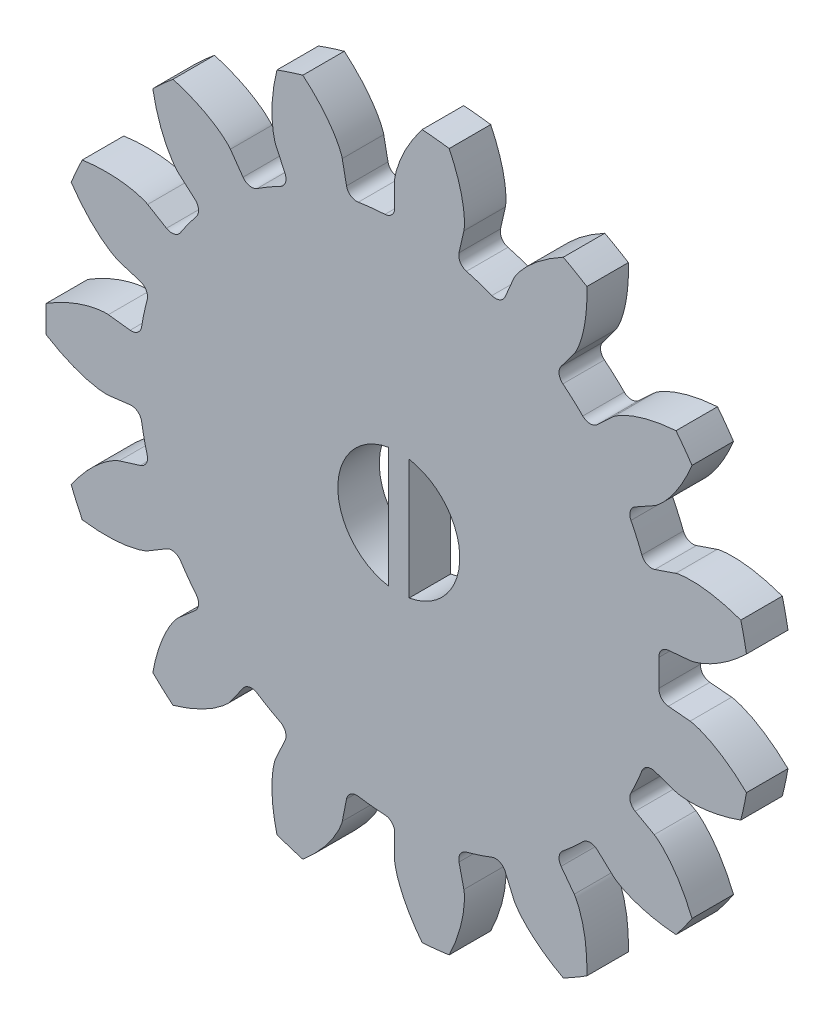
SolidWorks part; units mm, degrees
ref_plane "Front Plane" through (0, 0, 0) normal (0, 0, 1) x (1, 0, 0)
ref_plane "Top Plane" through (0, 0, 0) normal (0, 1, 0) x (1, 0, 0)
ref_plane "Right Plane" through (0, 0, 0) normal (1, 0, 0) x (0, 0, -1)
sketch "Model" plane through (0, 0, 0) normal (0, 0, 1) x (1, 0, 0)
  line L0 (-54.4812, -102.8312) -> (-54.9244, -103.7899)
  line L1 (-51.7248, -104.8295) -> (-51.5198, -103.7934)
  line L2 (-49.1951, -104.0377) -> (-49.2101, -105.0938)
  line L3 (-39.4416, -99.869) -> (-38.6668, -100.5867)
  line L4 (-40.5459, -102.2787) -> (-41.1787, -101.4331)
  line L5 (-57.1142, -102.5256) -> (-56.5055, -101.6625)
  line L6 (-43.8753, -102.9899) -> (-43.4594, -103.9608)
  line L7 (-58.8195, -99.5789) -> (-59.6143, -100.2745)
  line L8 (-45.8642, -104.7422) -> (-46.0984, -103.7123)
  line L9 (-36.6607, -95.2145) -> (-35.6609, -95.555)
  line L10 (-36.6894, -97.865) -> (-37.6114, -97.3499)
  line L11 (-36.0133, -89.8313) -> (-34.9614, -89.7357)
  line L12 (-34.9614, -92.2643) -> (-36.0133, -92.1687)
  line L13 (-51.5198, -78.2066) -> (-51.7248, -77.1705)
  line L14 (-54.9244, -78.2101) -> (-54.4812, -79.1688)
  line L15 (-49.2101, -76.9062) -> (-49.1951, -77.9623)
  line L16 (-56.5055, -80.3375) -> (-57.1142, -79.4744)
  line L17 (-62.4689, -86.8446) -> (-61.4599, -87.1567)
  line L18 (-60.1934, -84.3121) -> (-61.1006, -83.7712)
  line L19 (-61.4599, -94.8433) -> (-62.4689, -95.1554)
  line L20 (-62.9947, -92.6821) -> (-61.9459, -92.5569)
  line L21 (-59.6143, -81.7255) -> (-58.8195, -82.4211)
  line L22 (-61.9459, -89.4431) -> (-62.9947, -89.3179)
  line L23 (-61.1006, -98.2288) -> (-60.1934, -97.6879)
  line L24 (-43.4594, -78.0392) -> (-43.8753, -79.0101)
  line L25 (-46.0984, -78.2877) -> (-45.8642, -77.2578)
  line L26 (-38.6668, -81.4133) -> (-39.4416, -82.131)
  line L27 (-35.6609, -86.445) -> (-36.6607, -86.7855)
  line L28 (-37.6114, -84.6501) -> (-36.6894, -84.135)
  line L29 (-41.1787, -80.5669) -> (-40.5459, -79.7213)
  line L30 (-48.5, -93.8946) -> (-48.5, -88.1054)
  line L31 (-49.5, -88.1054) -> (-49.5, -93.8946)
  arc A0 (-55.825, -101.531) -> (-54.7076, -102.1761) centre (-49, -91) ccw
  arc A1 (-45.7407, -103.1186) -> (-46.0984, -103.7123) centre (-45.6109, -103.6014) ccw
  arc A2 (-54.4812, -102.8312) -> (-54.7076, -102.1761) centre (-54.935, -102.6214) ccw
  arc A3 (-50.9516, -103.3965) -> (-51.5198, -103.7934) centre (-51.0293, -103.8904) ccw
  arc A4 (-43.8753, -102.9899) -> (-44.5137, -102.7199) centre (-44.3349, -103.1868) ccw
  arc A5 (-41.0934, -100.7452) -> (-40.1347, -99.8819) centre (-49, -91) ccw
  arc A6 (-41.0746, -106.0396) -> (-39.938, -105.3833) centre (-49, -91) ccw
  arc A7 (-54.8735, -106.9531) -> (-53.6253, -107.3587) centre (-49, -91) ccw
  arc A8 (-35.6427, -101.5158) -> (-34.8712, -100.454) centre (-49, -91) ccw
  arc A9 (-41.0934, -100.7452) -> (-41.1787, -101.4331) centre (-40.7784, -101.1335) ccw
  arc A10 (-37.8133, -96.6868) -> (-37.6114, -97.3499) centre (-37.3676, -96.9134) ccw
  arc A11 (-55.825, -101.531) -> (-56.5055, -101.6625) centre (-56.0969, -101.9506) ccw
  arc A12 (-45.7407, -103.1186) -> (-44.5137, -102.7199) centre (-49, -91) ccw
  arc A13 (-59.5183, -97.8446) -> (-58.7599, -98.8884) centre (-49, -91) ccw
  arc A14 (-50.9516, -103.3965) -> (-49.6685, -103.5314) centre (-49, -91) ccw
  arc A15 (-58.8195, -99.5789) -> (-58.7599, -98.8884) centre (-59.1488, -99.2027) ccw
  arc A16 (-47.877, -107.9629) -> (-46.5717, -107.8257) centre (-49, -91) ccw
  arc A17 (-60.8544, -103.1849) -> (-59.8791, -104.0631) centre (-49, -91) ccw
  arc A18 (-37.8133, -96.6868) -> (-37.2885, -95.5081) centre (-49, -91) ccw
  arc A19 (-32.5203, -95.1738) -> (-32.2474, -93.89) centre (-49, -91) ccw
  arc A20 (-32.2474, -88.11) -> (-32.5203, -86.8262) centre (-49, -91) ccw
  arc A21 (-39.4416, -99.869) -> (-40.1347, -99.8819) centre (-39.7814, -100.2358) ccw
  arc A22 (-36.6607, -95.2145) -> (-37.2885, -95.5081) centre (-36.8219, -95.6878) ccw
  arc A23 (-49.1951, -104.0377) -> (-49.6685, -103.5314) centre (-49.6951, -104.0307) ccw
  arc A24 (-36.0133, -89.8313) -> (-36.4674, -90.3549) centre (-35.9681, -90.3292) ccw
  arc A25 (-36.4674, -91.6451) -> (-36.4674, -90.3549) centre (-49, -91) ccw
  arc A26 (-36.4674, -91.6451) -> (-36.0133, -92.1687) centre (-35.9681, -91.6708) ccw
  arc A27 (-49.6685, -78.4686) -> (-49.1951, -77.9623) centre (-49.6951, -77.9693) ccw
  arc A28 (-51.5198, -78.2066) -> (-50.9516, -78.6035) centre (-51.0293, -78.1096) ccw
  arc A29 (-53.6253, -74.6413) -> (-54.8735, -75.0469) centre (-49, -91) ccw
  arc A30 (-54.7076, -79.8239) -> (-54.4812, -79.1688) centre (-54.935, -79.3786) ccw
  arc A31 (-54.7076, -79.8239) -> (-55.825, -80.469) centre (-49, -91) ccw
  arc A32 (-56.5055, -80.3375) -> (-55.825, -80.469) centre (-56.0969, -80.0494) ccw
  arc A33 (-49.6685, -78.4686) -> (-50.9516, -78.6035) centre (-49, -91) ccw
  arc A34 (-46.5717, -74.1743) -> (-47.877, -74.0371) centre (-49, -91) ccw
  arc A35 (-58.7599, -83.1116) -> (-59.5183, -84.1554) centre (-49, -91) ccw
  arc A36 (-61.3929, -92.9747) -> (-61.9459, -92.5569) centre (-61.8866, -93.0534) ccw
  arc A37 (-61.3929, -92.9747) -> (-61.1246, -94.2367) centre (-49, -91) ccw
  arc A38 (-58.7599, -83.1116) -> (-58.8195, -82.4211) centre (-59.1488, -82.7973) ccw
  arc A39 (-61.9459, -89.4431) -> (-61.3929, -89.0253) centre (-61.8866, -88.9466) ccw
  arc A40 (-59.8791, -77.9369) -> (-60.8544, -78.8151) centre (-49, -91) ccw
  arc A41 (-64.2518, -83.4911) -> (-64.7856, -84.6901) centre (-49, -91) ccw
  arc A42 (-61.1246, -87.7633) -> (-61.4599, -87.1567) centre (-61.6077, -87.6344) ccw
  arc A43 (-65.9873, -90.3438) -> (-65.9873, -91.6562) centre (-49, -91) ccw
  arc A44 (-61.1246, -87.7633) -> (-61.3929, -89.0253) centre (-49, -91) ccw
  arc A45 (-60.1934, -84.3121) -> (-59.5183, -84.1554) centre (-59.9374, -83.8827) ccw
  arc A46 (-61.4599, -94.8433) -> (-61.1246, -94.2367) centre (-61.6077, -94.3656) ccw
  arc A47 (-59.5183, -97.8446) -> (-60.1934, -97.6879) centre (-59.9374, -98.1173) ccw
  arc A48 (-46.0984, -78.2877) -> (-45.7407, -78.8814) centre (-45.6109, -78.3986) ccw
  arc A49 (-39.938, -76.6167) -> (-41.0746, -75.9604) centre (-49, -91) ccw
  arc A50 (-44.5137, -79.2801) -> (-45.7407, -78.8814) centre (-49, -91) ccw
  arc A51 (-44.5137, -79.2801) -> (-43.8753, -79.0101) centre (-44.3349, -78.8132) ccw
  arc A52 (-37.2885, -86.4919) -> (-36.6607, -86.7855) centre (-36.8219, -86.3122) ccw
  arc A53 (-64.7856, -97.3099) -> (-64.2518, -98.5089) centre (-49, -91) ccw
  arc A54 (-37.6114, -84.6501) -> (-37.8133, -85.3132) centre (-37.3676, -85.0866) ccw
  arc A55 (-37.2885, -86.4919) -> (-37.8133, -85.3132) centre (-49, -91) ccw
  arc A56 (-40.1347, -82.1181) -> (-39.4416, -82.131) centre (-39.7814, -81.7642) ccw
  arc A57 (-34.8712, -81.546) -> (-35.6427, -80.4842) centre (-49, -91) ccw
  arc A58 (-40.1347, -82.1181) -> (-41.0934, -81.2548) centre (-49, -91) ccw
  arc A59 (-41.1787, -80.5669) -> (-41.0934, -81.2548) centre (-40.7784, -80.8665) ccw
  arc A60 (-48.5, -93.8946) -> (-48.5, -88.1054) centre (-49, -91) ccw
  arc A61 (-49.5, -88.1054) -> (-49.5, -93.8946) centre (-49, -91) ccw
  spline S0 degree 5 poles (-54.9244, -103.7899) (-54.9388, -103.8212) (-54.9546, -103.8611) (-54.9775, -103.9347) (-54.9977, -104.0186) (-55.0256, -104.1367) (-55.0449, -104.2305) (-55.0644, -104.3516) (-55.078, -104.4564) (-55.0915, -104.5796) (-55.1037, -104.7214) (-55.1126, -104.9005) (-55.1163, -105.0811) (-55.113, -105.2998) (-55.1005, -105.5479) (-55.0799, -105.7886) (-55.0514, -106.0308) (-55.0132, -106.2836) (-54.9706, -106.5187) (-54.9333, -106.6979) (-54.9032, -106.8302) (-54.8828, -106.9153) (-54.8735, -106.9531) knots 0 0 0 0 0 0 0.057143 0.071429 0.128571 0.142857 0.2 0.214286 0.271429 0.3 0.342857 0.428571 0.5 0.557143 0.642857 0.728571 0.8 0.871429 0.942857 1 1 1 1 1 1
  spline S1 degree 5 poles (-49.2101, -105.0938) (-49.2106, -105.1283) (-49.2087, -105.1711) (-49.1997, -105.2477) (-49.184, -105.3326) (-49.1614, -105.4518) (-49.141, -105.5454) (-49.1095, -105.6639) (-49.0793, -105.7652) (-49.0416, -105.8832) (-48.995, -106.0177) (-48.9303, -106.1849) (-48.8602, -106.3514) (-48.7683, -106.5499) (-48.6559, -106.7714) (-48.5392, -106.983) (-48.4147, -107.1926) (-48.2769, -107.4081) (-48.1424, -107.6055) (-48.0354, -107.754) (-47.9541, -107.8626) (-47.9008, -107.9321) (-47.877, -107.9629) knots 0 0 0 0 0 0 0.057143 0.071429 0.128571 0.142857 0.2 0.214286 0.271429 0.3 0.342857 0.428571 0.5 0.557143 0.642857 0.728571 0.8 0.871429 0.942857 1 1 1 1 1 1
  spline S2 degree 5 poles (-45.8642, -104.7422) (-45.8566, -104.7758) (-45.8495, -104.8181) (-45.8424, -104.8949) (-45.8401, -104.9811) (-45.8374, -105.1024) (-45.838, -105.1982) (-45.8441, -105.3207) (-45.8525, -105.4261) (-45.8649, -105.5493) (-45.8825, -105.6906) (-45.9111, -105.8676) (-45.945, -106.045) (-45.9936, -106.2583) (-46.0575, -106.4983) (-46.1276, -106.7295) (-46.2059, -106.9605) (-46.2959, -107.1998) (-46.3864, -107.4209) (-46.4602, -107.5884) (-46.5171, -107.7116) (-46.5548, -107.7906) (-46.5717, -107.8257) knots 0 0 0 0 0 0 0.057143 0.071429 0.128571 0.142857 0.2 0.214286 0.271429 0.3 0.342857 0.428571 0.5 0.557143 0.642857 0.728571 0.8 0.871429 0.942857 1 1 1 1 1 1
  spline S3 degree 5 poles (-38.6668, -100.5867) (-38.6415, -100.6101) (-38.6084, -100.6374) (-38.5455, -100.682) (-38.4719, -100.7271) (-38.3682, -100.7901) (-38.285, -100.8375) (-38.1758, -100.8934) (-38.0804, -100.9388) (-37.9674, -100.9897) (-37.8364, -101.0451) (-37.6688, -101.1089) (-37.4982, -101.1682) (-37.2892, -101.2327) (-37.0493, -101.2975) (-36.814, -101.3523) (-36.5749, -101.4) (-36.3226, -101.4418) (-36.0859, -101.4739) (-35.9039, -101.4938) (-35.7688, -101.506) (-35.6815, -101.5129) (-35.6427, -101.5158) knots 0 0 0 0 0 0 0.057143 0.071429 0.128571 0.142857 0.2 0.214286 0.271429 0.3 0.342857 0.428571 0.5 0.557143 0.642857 0.728571 0.8 0.871429 0.942857 1 1 1 1 1 1
  spline S4 degree 5 poles (-51.7248, -104.8295) (-51.7315, -104.8633) (-51.7422, -104.9048) (-51.7669, -104.9779) (-51.7999, -105.0576) (-51.8468, -105.1696) (-51.8863, -105.2568) (-51.9417, -105.3662) (-51.9923, -105.4591) (-52.0537, -105.5666) (-52.1272, -105.6885) (-52.2253, -105.8386) (-52.3285, -105.9869) (-52.4596, -106.1619) (-52.6156, -106.3553) (-52.7737, -106.5379) (-52.9392, -106.7171) (-53.1187, -106.8992) (-53.2914, -107.0643) (-53.4269, -107.1873) (-53.529, -107.2767) (-53.5955, -107.3335) (-53.6253, -107.3587) knots 0 0 0 0 0 0 0.057143 0.071429 0.128571 0.142857 0.2 0.214286 0.271429 0.3 0.342857 0.428571 0.5 0.557143 0.642857 0.728571 0.8 0.871429 0.942857 1 1 1 1 1 1
  spline S5 degree 5 poles (-57.1142, -102.5256) (-57.134, -102.5538) (-57.1607, -102.5873) (-57.2131, -102.644) (-57.2756, -102.7035) (-57.364, -102.7866) (-57.4355, -102.8503) (-57.5307, -102.9277) (-57.6146, -102.9919) (-57.7145, -103.0652) (-57.8312, -103.1466) (-57.9819, -103.2439) (-58.1364, -103.3374) (-58.3274, -103.4439) (-58.5486, -103.5571) (-58.7673, -103.6597) (-58.9913, -103.756) (-59.2294, -103.8494) (-59.4543, -103.93) (-59.6281, -103.9873) (-59.7577, -104.0274) (-59.8416, -104.0523) (-59.8791, -104.0631) knots 0 0 0 0 0 0 0.057143 0.071429 0.128571 0.142857 0.2 0.214286 0.271429 0.3 0.342857 0.428571 0.5 0.557143 0.642857 0.728571 0.8 0.871429 0.942857 1 1 1 1 1 1
  spline S6 degree 5 poles (-40.5459, -102.2787) (-40.5253, -102.3062) (-40.5016, -102.342) (-40.4638, -102.4093) (-40.4267, -102.4871) (-40.3748, -102.5969) (-40.3364, -102.6846) (-40.2922, -102.799) (-40.257, -102.8987) (-40.2182, -103.0163) (-40.1768, -103.1525) (-40.1309, -103.3258) (-40.0897, -103.5017) (-40.0475, -103.7163) (-40.0081, -103.9616) (-39.9782, -104.2013) (-39.9558, -104.4441) (-39.9406, -104.6994) (-39.9334, -104.9382) (-39.9326, -105.1213) (-39.9345, -105.2569) (-39.9368, -105.3444) (-39.938, -105.3833) knots 0 0 0 0 0 0 0.057143 0.071429 0.128571 0.142857 0.2 0.214286 0.271429 0.3 0.342857 0.428571 0.5 0.557143 0.642857 0.728571 0.8 0.871429 0.942857 1 1 1 1 1 1
  spline S7 degree 5 poles (-43.4594, -103.9608) (-43.4459, -103.9925) (-43.4267, -104.0308) (-43.3874, -104.0972) (-43.3385, -104.1683) (-43.2694, -104.268) (-43.2126, -104.3452) (-43.1357, -104.4407) (-43.0669, -104.521) (-42.9844, -104.6134) (-42.8872, -104.7173) (-42.7601, -104.8438) (-42.6283, -104.9674) (-42.4636, -105.1113) (-42.2709, -105.268) (-42.0782, -105.4138) (-41.8791, -105.5546) (-41.6657, -105.6954) (-41.4625, -105.821) (-41.3043, -105.9132) (-41.1859, -105.9794) (-41.109, -106.0211) (-41.0746, -106.0396) knots 0 0 0 0 0 0 0.057143 0.071429 0.128571 0.142857 0.2 0.214286 0.271429 0.3 0.342857 0.428571 0.5 0.557143 0.642857 0.728571 0.8 0.871429 0.942857 1 1 1 1 1 1
  spline S8 degree 5 poles (-35.6609, -95.555) (-35.6283, -95.5661) (-35.587, -95.5776) (-35.5113, -95.5927) (-35.4258, -95.604) (-35.3054, -95.6194) (-35.2101, -95.6288) (-35.0876, -95.6355) (-34.982, -95.6382) (-34.8581, -95.6387) (-34.7158, -95.636) (-34.5367, -95.6261) (-34.3567, -95.6109) (-34.1396, -95.5848) (-33.8941, -95.5464) (-33.6569, -95.5008) (-33.419, -95.4471) (-33.1716, -95.3827) (-32.9422, -95.3157) (-32.7679, -95.2599) (-32.6395, -95.2161) (-32.557, -95.1869) (-32.5203, -95.1738) knots 0 0 0 0 0 0 0.057143 0.071429 0.128571 0.142857 0.2 0.214286 0.271429 0.3 0.342857 0.428571 0.5 0.557143 0.642857 0.728571 0.8 0.871429 0.942857 1 1 1 1 1 1
  spline S9 degree 5 poles (-36.6894, -97.865) (-36.6593, -97.8818) (-36.6231, -97.9048) (-36.5613, -97.9509) (-36.4956, -98.0069) (-36.4037, -98.0861) (-36.3329, -98.1506) (-36.246, -98.2371) (-36.1733, -98.3139) (-36.09, -98.4056) (-35.9968, -98.5132) (-35.8843, -98.6528) (-35.7752, -98.7968) (-35.6493, -98.9756) (-35.5136, -99.1837) (-35.3887, -99.3905) (-35.2695, -99.6032) (-35.1517, -99.8302) (-35.0481, -100.0455) (-34.9729, -100.2124) (-34.9195, -100.3371) (-34.886, -100.4179) (-34.8712, -100.454) knots 0 0 0 0 0 0 0.057143 0.071429 0.128571 0.142857 0.2 0.214286 0.271429 0.3 0.342857 0.428571 0.5 0.557143 0.642857 0.728571 0.8 0.871429 0.942857 1 1 1 1 1 1
  spline S10 degree 5 poles (-34.9614, -89.7357) (-34.9271, -89.7326) (-34.8847, -89.7263) (-34.8094, -89.7093) (-34.7267, -89.6848) (-34.6105, -89.6499) (-34.5196, -89.6198) (-34.405, -89.5761) (-34.3074, -89.5355) (-34.194, -89.4856) (-34.0651, -89.4253) (-33.9055, -89.3434) (-33.7473, -89.2563) (-33.5595, -89.1442) (-33.3509, -89.0093) (-33.1527, -88.8711) (-32.9573, -88.7253) (-32.7574, -88.5658) (-32.5751, -88.4113) (-32.4386, -88.2894) (-32.3391, -88.1972) (-32.2756, -88.137) (-32.2474, -88.11) knots 0 0 0 0 0 0 0.057143 0.071429 0.128571 0.142857 0.2 0.214286 0.271429 0.3 0.342857 0.428571 0.5 0.557143 0.642857 0.728571 0.8 0.871429 0.942857 1 1 1 1 1 1
  spline S11 degree 5 poles (-34.9614, -92.2643) (-34.9271, -92.2674) (-34.8847, -92.2737) (-34.8094, -92.2907) (-34.7267, -92.3152) (-34.6105, -92.3501) (-34.5196, -92.3802) (-34.405, -92.4239) (-34.3074, -92.4645) (-34.194, -92.5144) (-34.0651, -92.5747) (-33.9055, -92.6566) (-33.7473, -92.7437) (-33.5595, -92.8558) (-33.3509, -92.9907) (-33.1527, -93.1289) (-32.9573, -93.2747) (-32.7574, -93.4342) (-32.5751, -93.5887) (-32.4386, -93.7106) (-32.3391, -93.8028) (-32.2756, -93.863) (-32.2474, -93.89) knots 0 0 0 0 0 0 0.057143 0.071429 0.128571 0.142857 0.2 0.214286 0.271429 0.3 0.342857 0.428571 0.5 0.557143 0.642857 0.728571 0.8 0.871429 0.942857 1 1 1 1 1 1
  spline S12 degree 5 poles (-45.8642, -77.2578) (-45.8566, -77.2242) (-45.8495, -77.1819) (-45.8424, -77.1051) (-45.8401, -77.0189) (-45.8374, -76.8976) (-45.838, -76.8018) (-45.8441, -76.6793) (-45.8525, -76.5739) (-45.8649, -76.4507) (-45.8825, -76.3094) (-45.9111, -76.1324) (-45.945, -75.955) (-45.9936, -75.7417) (-46.0575, -75.5017) (-46.1276, -75.2705) (-46.2059, -75.0395) (-46.2959, -74.8002) (-46.3864, -74.5791) (-46.4602, -74.4116) (-46.5171, -74.2884) (-46.5548, -74.2094) (-46.5717, -74.1743) knots 0 0 0 0 0 0 0.057143 0.071429 0.128571 0.142857 0.2 0.214286 0.271429 0.3 0.342857 0.428571 0.5 0.557143 0.642857 0.728571 0.8 0.871429 0.942857 1 1 1 1 1 1
  spline S13 degree 5 poles (-49.2101, -76.9062) (-49.2106, -76.8717) (-49.2087, -76.8289) (-49.1997, -76.7523) (-49.184, -76.6674) (-49.1614, -76.5482) (-49.141, -76.4546) (-49.1095, -76.3361) (-49.0793, -76.2348) (-49.0416, -76.1168) (-48.995, -75.9823) (-48.9303, -75.8151) (-48.8602, -75.6486) (-48.7683, -75.4501) (-48.6559, -75.2286) (-48.5392, -75.017) (-48.4147, -74.8074) (-48.2769, -74.5919) (-48.1424, -74.3945) (-48.0354, -74.246) (-47.9541, -74.1374) (-47.9008, -74.0679) (-47.877, -74.0371) knots 0 0 0 0 0 0 0.057143 0.071429 0.128571 0.142857 0.2 0.214286 0.271429 0.3 0.342857 0.428571 0.5 0.557143 0.642857 0.728571 0.8 0.871429 0.942857 1 1 1 1 1 1
  spline S14 degree 5 poles (-54.9244, -78.2101) (-54.9388, -78.1788) (-54.9546, -78.1389) (-54.9775, -78.0653) (-54.9977, -77.9814) (-55.0256, -77.8633) (-55.0449, -77.7695) (-55.0644, -77.6484) (-55.078, -77.5436) (-55.0915, -77.4204) (-55.1037, -77.2786) (-55.1126, -77.0995) (-55.1163, -76.9189) (-55.113, -76.7002) (-55.1005, -76.4521) (-55.0799, -76.2114) (-55.0514, -75.9692) (-55.0132, -75.7164) (-54.9706, -75.4813) (-54.9333, -75.3021) (-54.9032, -75.1698) (-54.8828, -75.0847) (-54.8735, -75.0469) knots 0 0 0 0 0 0 0.057143 0.071429 0.128571 0.142857 0.2 0.214286 0.271429 0.3 0.342857 0.428571 0.5 0.557143 0.642857 0.728571 0.8 0.871429 0.942857 1 1 1 1 1 1
  spline S15 degree 5 poles (-51.7248, -77.1705) (-51.7315, -77.1367) (-51.7422, -77.0952) (-51.7669, -77.0221) (-51.7999, -76.9424) (-51.8468, -76.8304) (-51.8863, -76.7432) (-51.9417, -76.6338) (-51.9923, -76.5409) (-52.0537, -76.4334) (-52.1272, -76.3115) (-52.2253, -76.1614) (-52.3285, -76.0131) (-52.4596, -75.8381) (-52.6156, -75.6447) (-52.7737, -75.4621) (-52.9392, -75.2829) (-53.1187, -75.1008) (-53.2914, -74.9357) (-53.4269, -74.8127) (-53.529, -74.7233) (-53.5955, -74.6665) (-53.6253, -74.6413) knots 0 0 0 0 0 0 0.057143 0.071429 0.128571 0.142857 0.2 0.214286 0.271429 0.3 0.342857 0.428571 0.5 0.557143 0.642857 0.728571 0.8 0.871429 0.942857 1 1 1 1 1 1
  spline S16 degree 5 poles (-57.1142, -79.4744) (-57.134, -79.4462) (-57.1607, -79.4127) (-57.2131, -79.356) (-57.2756, -79.2965) (-57.364, -79.2134) (-57.4355, -79.1497) (-57.5307, -79.0723) (-57.6146, -79.0081) (-57.7145, -78.9348) (-57.8312, -78.8534) (-57.9819, -78.7561) (-58.1364, -78.6626) (-58.3274, -78.5561) (-58.5486, -78.4429) (-58.7673, -78.3403) (-58.9913, -78.244) (-59.2294, -78.1506) (-59.4543, -78.07) (-59.6281, -78.0127) (-59.7577, -77.9726) (-59.8416, -77.9477) (-59.8791, -77.9369) knots 0 0 0 0 0 0 0.057143 0.071429 0.128571 0.142857 0.2 0.214286 0.271429 0.3 0.342857 0.428571 0.5 0.557143 0.642857 0.728571 0.8 0.871429 0.942857 1 1 1 1 1 1
  spline S17 degree 5 poles (-61.1006, -83.7712) (-61.1302, -83.7535) (-61.1682, -83.7337) (-61.2391, -83.7032) (-61.3204, -83.6744) (-61.4349, -83.6343) (-61.5262, -83.6052) (-61.6446, -83.5732) (-61.7474, -83.5487) (-61.8685, -83.5224) (-62.0082, -83.4955) (-62.1854, -83.4679) (-62.3646, -83.4453) (-62.5824, -83.4257) (-62.8305, -83.4122) (-63.072, -83.4075) (-63.3159, -83.4106) (-63.5713, -83.4222) (-63.8096, -83.44) (-63.9917, -83.4584) (-64.1264, -83.4745) (-64.2132, -83.4859) (-64.2518, -83.4911) knots 0 0 0 0 0 0 0.057143 0.071429 0.128571 0.142857 0.2 0.214286 0.271429 0.3 0.342857 0.428571 0.5 0.557143 0.642857 0.728571 0.8 0.871429 0.942857 1 1 1 1 1 1
  spline S18 degree 5 poles (-62.9947, -89.3179) (-63.0289, -89.3138) (-63.0717, -89.3112) (-63.1488, -89.3121) (-63.2348, -89.3188) (-63.3558, -89.3288) (-63.451, -89.3394) (-63.5721, -89.3583) (-63.676, -89.3777) (-63.7973, -89.4029) (-63.9359, -89.4352) (-64.109, -89.4821) (-64.2819, -89.5343) (-64.4889, -89.605) (-64.721, -89.6936) (-64.9436, -89.7875) (-65.1651, -89.8895) (-65.3938, -90.004) (-65.6041, -90.1172) (-65.7631, -90.2081) (-65.8796, -90.2775) (-65.9542, -90.3232) (-65.9873, -90.3438) knots 0 0 0 0 0 0 0.057143 0.071429 0.128571 0.142857 0.2 0.214286 0.271429 0.3 0.342857 0.428571 0.5 0.557143 0.642857 0.728571 0.8 0.871429 0.942857 1 1 1 1 1 1
  spline S19 degree 5 poles (-62.9947, -92.6821) (-63.0289, -92.6862) (-63.0717, -92.6888) (-63.1488, -92.6879) (-63.2348, -92.6812) (-63.3558, -92.6712) (-63.451, -92.6606) (-63.5721, -92.6417) (-63.676, -92.6223) (-63.7973, -92.5971) (-63.9359, -92.5648) (-64.109, -92.5179) (-64.2819, -92.4657) (-64.4889, -92.395) (-64.721, -92.3064) (-64.9436, -92.2125) (-65.1651, -92.1105) (-65.3938, -91.996) (-65.6041, -91.8828) (-65.7631, -91.7919) (-65.8796, -91.7225) (-65.9542, -91.6768) (-65.9873, -91.6562) knots 0 0 0 0 0 0 0.057143 0.071429 0.128571 0.142857 0.2 0.214286 0.271429 0.3 0.342857 0.428571 0.5 0.557143 0.642857 0.728571 0.8 0.871429 0.942857 1 1 1 1 1 1
  spline S20 degree 5 poles (-59.6143, -81.7255) (-59.6402, -81.7028) (-59.6708, -81.6728) (-59.7217, -81.6148) (-59.7743, -81.5464) (-59.8478, -81.4498) (-59.9036, -81.372) (-59.9707, -81.2693) (-60.0258, -81.1791) (-60.0882, -81.0721) (-60.157, -80.9475) (-60.238, -80.7875) (-60.3148, -80.624) (-60.4008, -80.4229) (-60.4903, -80.1912) (-60.5694, -79.9629) (-60.6418, -79.73) (-60.7097, -79.4835) (-60.7664, -79.2514) (-60.8052, -79.0725) (-60.8315, -78.9395) (-60.8475, -78.8534) (-60.8544, -78.8151) knots 0 0 0 0 0 0 0.057143 0.071429 0.128571 0.142857 0.2 0.214286 0.271429 0.3 0.342857 0.428571 0.5 0.557143 0.642857 0.728571 0.8 0.871429 0.942857 1 1 1 1 1 1
  spline S21 degree 5 poles (-62.4689, -86.8446) (-62.5019, -86.8344) (-62.542, -86.8194) (-62.6121, -86.7871) (-62.688, -86.746) (-62.7944, -86.6877) (-62.877, -86.6393) (-62.98, -86.5727) (-63.0671, -86.5127) (-63.1676, -86.4404) (-63.2811, -86.3545) (-63.4202, -86.2413) (-63.5569, -86.1232) (-63.7172, -85.9745) (-63.8932, -85.7991) (-64.0583, -85.6228) (-64.2192, -85.4395) (-64.3815, -85.2419) (-64.5277, -85.053) (-64.6359, -84.9053) (-64.7141, -84.7945) (-64.7637, -84.7223) (-64.7856, -84.6901) knots 0 0 0 0 0 0 0.057143 0.071429 0.128571 0.142857 0.2 0.214286 0.271429 0.3 0.342857 0.428571 0.5 0.557143 0.642857 0.728571 0.8 0.871429 0.942857 1 1 1 1 1 1
  spline S22 degree 5 poles (-61.1006, -98.2288) (-61.1302, -98.2465) (-61.1682, -98.2663) (-61.2391, -98.2968) (-61.3204, -98.3256) (-61.4349, -98.3657) (-61.5262, -98.3948) (-61.6446, -98.4268) (-61.7474, -98.4513) (-61.8685, -98.4776) (-62.0082, -98.5045) (-62.1854, -98.5321) (-62.3646, -98.5547) (-62.5824, -98.5743) (-62.8305, -98.5878) (-63.072, -98.5925) (-63.3159, -98.5894) (-63.5713, -98.5778) (-63.8096, -98.56) (-63.9917, -98.5416) (-64.1264, -98.5255) (-64.2132, -98.5141) (-64.2518, -98.5089) knots 0 0 0 0 0 0 0.057143 0.071429 0.128571 0.142857 0.2 0.214286 0.271429 0.3 0.342857 0.428571 0.5 0.557143 0.642857 0.728571 0.8 0.871429 0.942857 1 1 1 1 1 1
  spline S23 degree 5 poles (-62.4689, -95.1554) (-62.5019, -95.1656) (-62.542, -95.1806) (-62.6121, -95.2129) (-62.688, -95.254) (-62.7944, -95.3123) (-62.877, -95.3607) (-62.98, -95.4273) (-63.0671, -95.4873) (-63.1676, -95.5596) (-63.2811, -95.6455) (-63.4202, -95.7587) (-63.5569, -95.8768) (-63.7172, -96.0255) (-63.8932, -96.2009) (-64.0583, -96.3772) (-64.2192, -96.5605) (-64.3815, -96.7581) (-64.5277, -96.947) (-64.6359, -97.0947) (-64.7141, -97.2055) (-64.7637, -97.2777) (-64.7856, -97.3099) knots 0 0 0 0 0 0 0.057143 0.071429 0.128571 0.142857 0.2 0.214286 0.271429 0.3 0.342857 0.428571 0.5 0.557143 0.642857 0.728571 0.8 0.871429 0.942857 1 1 1 1 1 1
  spline S24 degree 5 poles (-40.5459, -79.7213) (-40.5253, -79.6938) (-40.5016, -79.658) (-40.4638, -79.5907) (-40.4267, -79.5129) (-40.3748, -79.4031) (-40.3364, -79.3154) (-40.2922, -79.201) (-40.257, -79.1013) (-40.2182, -78.9837) (-40.1768, -78.8475) (-40.1309, -78.6742) (-40.0897, -78.4983) (-40.0475, -78.2837) (-40.0081, -78.0384) (-39.9782, -77.7987) (-39.9558, -77.5559) (-39.9406, -77.3006) (-39.9334, -77.0618) (-39.9326, -76.8787) (-39.9345, -76.7431) (-39.9368, -76.6556) (-39.938, -76.6167) knots 0 0 0 0 0 0 0.057143 0.071429 0.128571 0.142857 0.2 0.214286 0.271429 0.3 0.342857 0.428571 0.5 0.557143 0.642857 0.728571 0.8 0.871429 0.942857 1 1 1 1 1 1
  spline S25 degree 5 poles (-43.4594, -78.0392) (-43.4459, -78.0075) (-43.4267, -77.9692) (-43.3874, -77.9028) (-43.3385, -77.8317) (-43.2694, -77.732) (-43.2126, -77.6548) (-43.1357, -77.5593) (-43.0669, -77.479) (-42.9844, -77.3866) (-42.8872, -77.2827) (-42.7601, -77.1562) (-42.6283, -77.0326) (-42.4636, -76.8887) (-42.2709, -76.732) (-42.0782, -76.5862) (-41.8791, -76.4454) (-41.6657, -76.3046) (-41.4625, -76.179) (-41.3043, -76.0868) (-41.1859, -76.0206) (-41.109, -75.9789) (-41.0746, -75.9604) knots 0 0 0 0 0 0 0.057143 0.071429 0.128571 0.142857 0.2 0.214286 0.271429 0.3 0.342857 0.428571 0.5 0.557143 0.642857 0.728571 0.8 0.871429 0.942857 1 1 1 1 1 1
  spline S26 degree 5 poles (-36.6894, -84.135) (-36.6593, -84.1182) (-36.6231, -84.0952) (-36.5613, -84.0491) (-36.4956, -83.9931) (-36.4037, -83.9139) (-36.3329, -83.8494) (-36.246, -83.7629) (-36.1733, -83.6861) (-36.09, -83.5944) (-35.9968, -83.4868) (-35.8843, -83.3472) (-35.7752, -83.2032) (-35.6493, -83.0244) (-35.5136, -82.8163) (-35.3887, -82.6095) (-35.2695, -82.3968) (-35.1517, -82.1698) (-35.0481, -81.9545) (-34.9729, -81.7876) (-34.9195, -81.6629) (-34.886, -81.5821) (-34.8712, -81.546) knots 0 0 0 0 0 0 0.057143 0.071429 0.128571 0.142857 0.2 0.214286 0.271429 0.3 0.342857 0.428571 0.5 0.557143 0.642857 0.728571 0.8 0.871429 0.942857 1 1 1 1 1 1
  spline S27 degree 5 poles (-38.6668, -81.4133) (-38.6415, -81.3899) (-38.6084, -81.3626) (-38.5455, -81.318) (-38.4719, -81.2729) (-38.3682, -81.2099) (-38.285, -81.1625) (-38.1758, -81.1066) (-38.0804, -81.0612) (-37.9674, -81.0103) (-37.8364, -80.9549) (-37.6688, -80.8911) (-37.4982, -80.8318) (-37.2892, -80.7673) (-37.0493, -80.7025) (-36.814, -80.6477) (-36.5749, -80.6) (-36.3226, -80.5582) (-36.0859, -80.5261) (-35.9039, -80.5062) (-35.7688, -80.494) (-35.6815, -80.4871) (-35.6427, -80.4842) knots 0 0 0 0 0 0 0.057143 0.071429 0.128571 0.142857 0.2 0.214286 0.271429 0.3 0.342857 0.428571 0.5 0.557143 0.642857 0.728571 0.8 0.871429 0.942857 1 1 1 1 1 1
  spline S28 degree 5 poles (-35.6609, -86.445) (-35.6283, -86.4339) (-35.587, -86.4224) (-35.5113, -86.4073) (-35.4258, -86.396) (-35.3054, -86.3806) (-35.2101, -86.3712) (-35.0876, -86.3645) (-34.982, -86.3618) (-34.8581, -86.3613) (-34.7158, -86.364) (-34.5367, -86.3739) (-34.3567, -86.3891) (-34.1396, -86.4152) (-33.8941, -86.4536) (-33.6569, -86.4992) (-33.419, -86.5529) (-33.1716, -86.6173) (-32.9422, -86.6843) (-32.7679, -86.7401) (-32.6395, -86.7839) (-32.557, -86.8131) (-32.5203, -86.8262) knots 0 0 0 0 0 0 0.057143 0.071429 0.128571 0.142857 0.2 0.214286 0.271429 0.3 0.342857 0.428571 0.5 0.557143 0.642857 0.728571 0.8 0.871429 0.942857 1 1 1 1 1 1
  spline S29 degree 5 poles (-59.6143, -100.2745) (-59.6402, -100.2972) (-59.6708, -100.3272) (-59.7217, -100.3852) (-59.7743, -100.4536) (-59.8478, -100.5502) (-59.9036, -100.628) (-59.9707, -100.7307) (-60.0258, -100.8209) (-60.0882, -100.9279) (-60.157, -101.0525) (-60.238, -101.2125) (-60.3148, -101.376) (-60.4008, -101.5771) (-60.4903, -101.8088) (-60.5694, -102.0371) (-60.6418, -102.27) (-60.7097, -102.5165) (-60.7664, -102.7486) (-60.8052, -102.9275) (-60.8315, -103.0605) (-60.8475, -103.1466) (-60.8544, -103.1849) knots 0 0 0 0 0 0 0.057143 0.071429 0.128571 0.142857 0.2 0.214286 0.271429 0.3 0.342857 0.428571 0.5 0.557143 0.642857 0.728571 0.8 0.871429 0.942857 1 1 1 1 1 1
extrude "Boss-Extrude1" add sketch "Model" along normal blind 2
